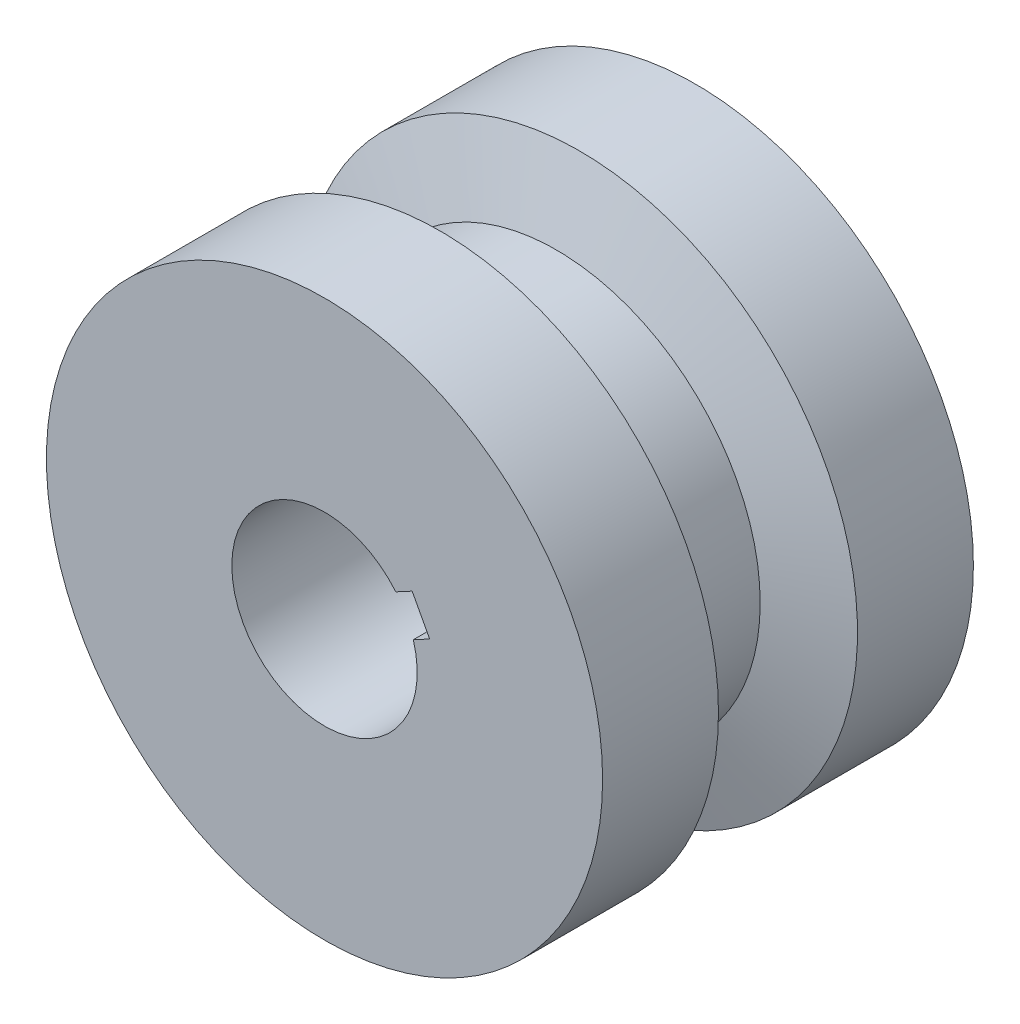
SolidWorks part; units mm, degrees
ref_plane "Front Plane" through (0, 0, 0) normal (0, 0, 1) x (1, 0, 0)
ref_plane "Top Plane" through (0, 0, 0) normal (0, 1, 0) x (1, 0, 0)
ref_plane "Right Plane" through (0, 0, 0) normal (1, 0, 0) x (0, 0, -1)
sketch "Sketch1" plane through (0, 0, 0) normal (0, 0, 1) x (1, 0, 0)
  circle A0 centre (0, 0) radius 2.5
  circle A1 centre (0, 0) radius 7.5
  dimension "D1" = 5
  dimension "D2" = 15
extrude "Boss-Extrude1" add sketch "Sketch1" along normal mid plane 10
sketch "Sketch3" plane through (0, 0, 0) normal (1, 0, 0) x (0, 0, -1)
  line L0 (-2.5, 9.5) -> (-1.25, 5.5)
  line L1 (-1.25, 5.5) -> (1.25, 5.5)
  line L2 (1.25, 5.5) -> (2.5, 9.5)
  line L3 (2.5, 9.5) -> (-2.5, 9.5)
  line L4 (-9.7476, 0) -> (7.006, 0) construction
  point P2 (0, 5.5)
  dimension "D1" = 4
  dimension "D2" = 2.5
  dimension "D3" = 5
  dimension "D4" = 9.5
revolve "Cut-Revolve1" cut sketch "Sketch3" angle 360 about L4
sketch "Sketch4" plane through (0, 0, -5) normal (0, 0, -1) x (-1, 0, 0)
  line L0 (-2.3953, 0.716) -> (-2.836, 0.9522)
  line L1 (-2.3953, 0.716) -> (-1.9545, 0.4799) construction
  line L2 (-2.836, 0.9522) -> (-2.3637, 1.8336)
  line L3 (-2.3637, 1.8336) -> (-1.923, 1.5975)
  line L4 (-1.4823, 1.3614) -> (-1.923, 1.5975) construction
  circle A0 centre (0, 0) radius 2.5 construction
  arc A1 (-2.3953, 0.716) -> (-1.923, 1.5975) centre (0, 0) cw
  dimension "D1" = 0.5
  dimension "D2" = 1
  dimension "D3" = 0.5
extrude "Cut-Extrude1" cut sketch "Sketch4" against normal blind 10
